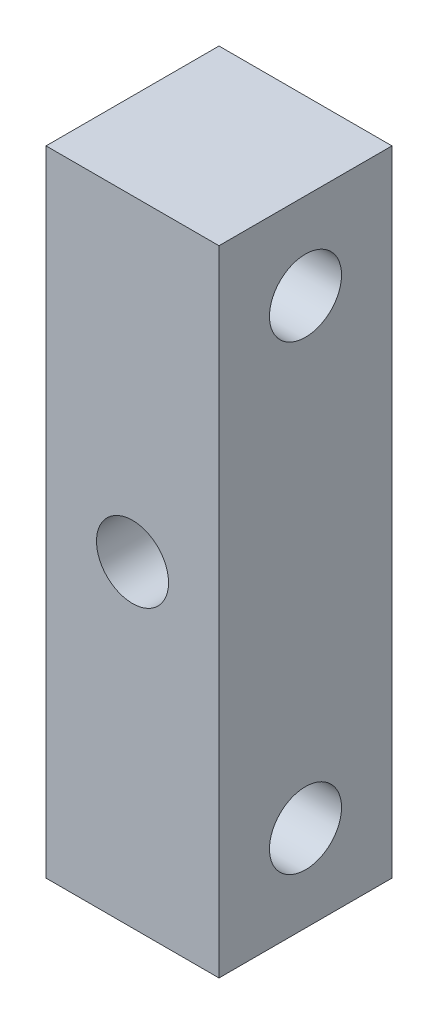
SolidWorks part; units mm, degrees
material "6061 合金"
ref_plane "前视基准面" through (0, 0, 0) normal (0, 0, 1) x (1, 0, 0)
ref_plane "上视基准面" through (0, 0, 0) normal (0, 1, 0) x (1, 0, 0)
ref_plane "右视基准面" through (0, 0, 0) normal (1, 0, 0) x (0, 0, -1)
sketch "草图1" plane through (0, 0, 0) normal (1, 0, 0) x (0, 0, -1)
  line L0 (0, 0) -> (3, 0) construction
  line L1 (-3, 11) -> (3, 11)
  line L2 (-3, 11) -> (-3, -11)
  line L3 (-3, -11) -> (3, -11)
  line L4 (3, 11) -> (3, -11)
  line L5 (-3, 11) -> (3, -11) construction
  line L6 (-3, -11) -> (3, 11) construction
  circle A0 centre (0, 8) radius 1.25
  circle A1 centre (0, -8) radius 1.25
  point P0 (0, 0)
  dimension "D1" = 2.5
  dimension "D2" = 16
  dimension "D3" = 6
  dimension "D4" = 3
extrude "凸台-拉伸1" add sketch "草图1" along normal blind 6
cosmetic thread "装饰螺纹线1" parameters "D2"=3
cosmetic thread "装饰螺纹线2" parameters "D2"=3
sketch "草图2" plane through (0, 0, 3) normal (0, 0, 1) x (1, 0, 0)
  line L0 (3, 11) -> (3, -11) construction
  line L1 (6, 11) -> (0, 11) construction
  line L2 (6, -11) -> (0, -11) construction
  circle A0 centre (3, 0) radius 1.25
  dimension "D1" = 2.5
extrude "切除-拉伸1" cut sketch "草图2" against normal through all
cosmetic thread "装饰螺纹线3" parameters "D2"=3
